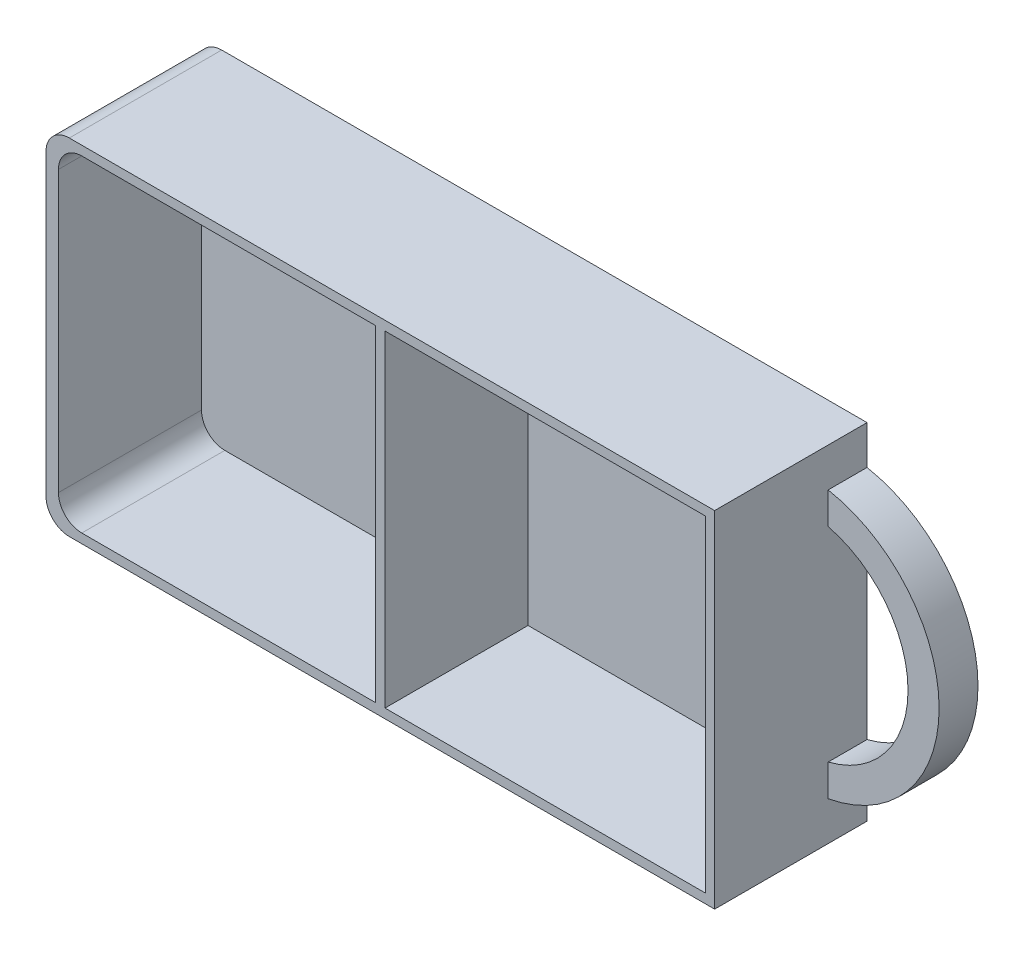
SolidWorks part; units mm, degrees
ref_plane "Спереди" through (0, 0, 0) normal (0, 0, 1) x (1, 0, 0)
ref_plane "Сверху" through (0, 0, 0) normal (0, 1, 0) x (1, 0, 0)
ref_plane "Справа" through (0, 0, 0) normal (1, 0, 0) x (0, 0, -1)
other "Configuration Table"
sketch "Эскиз1" plane through (0, 0, 0) normal (0, 0, 1) x (1, 0, 0)
  line L1 (-43, 22.2) -> (43, 22.2)
  line L2 (-43, 22.2) -> (-43, -22.2)
  line L3 (-43, -22.2) -> (43, -22.2)
  line L4 (43, 22.2) -> (43, -22.2)
  line L5 (-43, 22.2) -> (43, -22.2) construction
  line L6 (-43, -22.2) -> (43, 22.2) construction
  point P0 (0, 0)
  dimension "D1" = 86
  dimension "D2" = 44.4
extrude "Бобышка-Вытянуть1" add sketch "Эскиз1" along normal blind 19.6
sketch "Эскиз2" plane through (0, 0, 0) normal (0, 0, 1) x (1, 0, 0)
  line L0 (0, 0) -> (43, 0) construction
  line L1 (43, -22.2) -> (43, 22.2) construction
  line L2 (43, 17.2) -> (43, 13.1088)
  line L3 (43, -17.2) -> (43, -13.1088)
  arc A0 (43, -17.2) -> (43, 17.2) centre (39.7735, 0) ccw
  arc A1 (43, -13.1088) -> (43, 13.1088) centre (39.7735, 0) ccw
  dimension "D3" = 13.5
  dimension "D4" = 4
  dimension "D1" = 5
  dimension "D2" = 5
extrude "Бобышка-Вытянуть2" add sketch "Эскиз2" along normal blind 5
sketch "Эскиз3" plane through (0, 0, 19.6) normal (0, 0, 1) x (1, 0, 0)
  line L5 (-41.4, 22.2) -> (-41.4, -22.2)
  line L6 (-43, -21) -> (41.8, -21)
  line L7 (41.8, -21) -> (41.8, 21)
  line L8 (41.8, 21) -> (-43, 21)
  line L9 (-41.4, -21) -> (41.8, -21)
  line L10 (41.8, -21) -> (41.8, 21)
  line L11 (41.8, 21) -> (-41.4, 21)
  line L12 (-41.4, 21) -> (-41.4, -21)
  line L13 (-0.6, -21) -> (0.6, -21)
  line L14 (-0.6, -21) -> (-0.6, 21)
  line L15 (-0.6, 21) -> (0.6, 21)
  line L16 (0.6, -21) -> (0.6, 21)
  line L17 (-0.6, -21) -> (0.6, 21) construction
  line L18 (-0.6, 21) -> (0.6, -21) construction
  point P0 (0, 0)
  dimension "D3" = 1.2
  dimension "D4" = 40.8
  dimension "D5" = 41.2
  dimension "D6" = 42
  dimension "D1" = 1.2
  dimension "D2" = 1.6
extrude "Вырез-Вытянуть1" cut sketch "Эскиз3" against normal offset from surface (18.4 mm away) 1.2 contours L9 L14 L11 L12 | L16 L9 L10 L11 up to face at (48.1368, 0, 0)
fillet "Скругление1" radius 3 4 edges at (-43, 22.2, 9.8) (-43, -22.2, 9.8) (-41.4, -21, 10.4) (-41.4, 21, 10.4)
